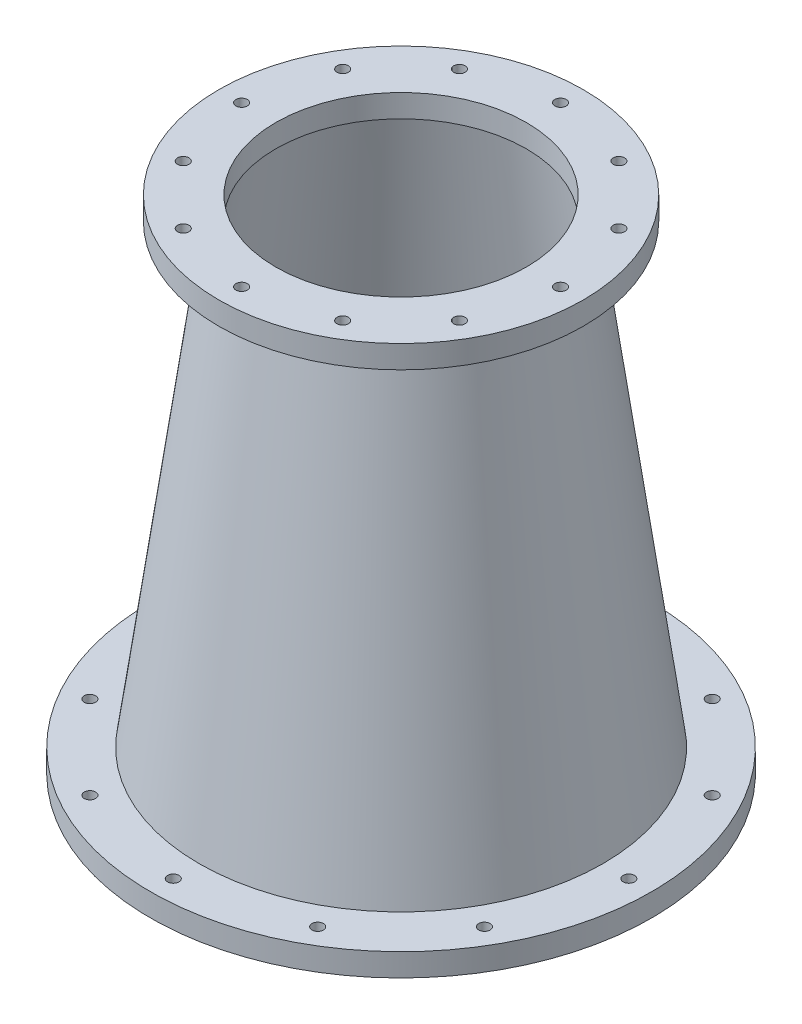
SolidWorks part; units mm, degrees
material "Plain Carbon Steel"
ref_plane "Front Plane" through (0, 0, 0) normal (0, 0, 1) x (1, 0, 0)
ref_plane "Top Plane" through (0, 0, 0) normal (0, 1, 0) x (1, 0, 0)
ref_plane "Right Plane" through (0, 0, 0) normal (1, 0, 0) x (0, 0, -1)
sketch "Sketch1" plane through (0, 0, 0) normal (0, 0, 1) x (1, 0, 0)
  line L0 (0, 279.4) -> (0, 0) construction
  line L1 (69.85, 279.4) -> (107.95, 0)
  line L2 (107.95, 0) -> (114.3, 0)
  line L3 (114.3, 0) -> (76.2, 279.4)
  line L4 (76.2, 279.4) -> (69.85, 279.4)
  dimension "D1" = 279.4
  dimension "D2" = 69.85
  dimension "D3" = 76.2
  dimension "D4" = 107.95
  dimension "D5" = 114.3
revolve "Revolve1" add sketch "Sketch1" angle 360 about L0
ref_plane "Plane1" through (0, 279.4, 0) normal (0, 1, 0) x (1, 0, 0)
sketch "Sketch2" plane through (0, 279.4, 0) normal (0, 1, 0) x (1, 0, 0)
  line L0 (0, 101.6) -> (0, -101.6) construction
  line L1 (-101.6, 0) -> (88.9, 0) construction
  circle A0 centre (0, 0) radius 101.6
  circle A1 centre (0, 0) radius 69.85 construction
  circle A2 centre (0, 0) radius 76.2 construction
  circle A3 centre (0, 0) radius 69.85
  circle A4 centre (0, 0) radius 76.2 construction
  circle A5 centre (0, 0) radius 88.9 construction
  circle A6 centre (0, 88.9) radius 3.175
  circle A7 centre (44.45, 76.9897) radius 3.175
  circle A8 centre (76.9897, 44.45) radius 3.175
  circle A9 centre (88.9, 0) radius 3.175
  circle A10 centre (76.9897, -44.45) radius 3.175
  circle A11 centre (44.45, -76.9897) radius 3.175
  circle A12 centre (0, -88.9) radius 3.175
  circle A13 centre (-44.45, -76.9897) radius 3.175
  circle A14 centre (-76.9897, -44.45) radius 3.175
  circle A15 centre (-88.9, 0) radius 3.175
  circle A16 centre (-76.9897, 44.45) radius 3.175
  circle A17 centre (-44.45, 76.9897) radius 3.175
  point P40 (0, 0)
  dimension "D1" = 203.2
  dimension "D2" = 177.8
  dimension "D3" = 6.35
  dimension "D4" = 12
extrude "Boss-Extrude1" add sketch "Sketch2" against normal blind 12.7 contours A14 | A16 | A17 | A8 | A9 | A10 | A11 | A12 | A13 | A0 | A3 | A15 | A6 | A7
ref_plane "Plane2" through (0, 0, 0) normal (0, -1, 0) x (-1, 0, 0)
sketch "Sketch3" plane through (0, 0, 0) normal (0, -1, 0) x (-1, 0, 0)
  line L0 (0, 139.7) -> (0, -139.7) construction
  line L1 (-139.7, 0) -> (139.7, 0) construction
  line L2 (0, 0) -> (0, 127) construction
  circle A0 centre (0, 0) radius 107.95 construction
  circle A1 centre (0, 0) radius 114.3 construction
  circle A2 centre (0, 0) radius 107.95
  circle A3 centre (0, 0) radius 114.3 construction
  circle A4 centre (0, 0) radius 139.7
  circle A5 centre (0, 0) radius 127 construction
  circle A6 centre (0, 127) radius 3.175
  circle A7 centre (63.5, 109.9852) radius 3.175
  circle A8 centre (109.9852, 63.5) radius 3.175
  circle A9 centre (127, 0) radius 3.175
  circle A10 centre (109.9852, -63.5) radius 3.175
  circle A11 centre (63.5, -109.9852) radius 3.175
  circle A12 centre (0, -127) radius 3.175
  circle A13 centre (-63.5, -109.9852) radius 3.175
  circle A14 centre (-109.9852, -63.5) radius 3.175
  circle A15 centre (-127, 0) radius 3.175
  circle A16 centre (-109.9852, 63.5) radius 3.175
  circle A17 centre (-63.5, 109.9852) radius 3.175
  dimension "D1" = 279.4
  dimension "D2" = 254
  dimension "D3" = 6.35
  dimension "D5" = 127
  dimension "D4" = 12
extrude "Boss-Extrude2" add sketch "Sketch3" against normal blind 12.7 contours A4 | A2 | A7 | A8 | A9 | A10 | A11 | A12 | A13 | A14 | A15 | A16 | A17 | A6
